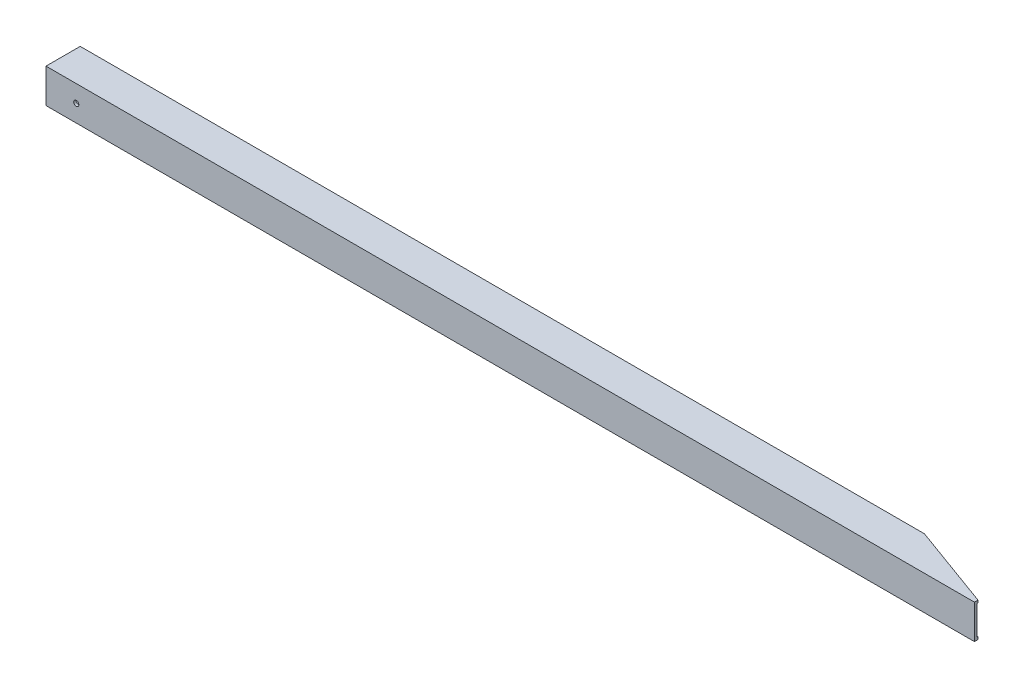
SolidWorks part; units mm, degrees
material "6061 Alloy"
ref_plane "Front Plane" through (0, 0, 0) normal (0, 0, 1) x (1, 0, 0)
ref_plane "Top Plane" through (0, 0, 0) normal (0, 1, 0) x (1, 0, 0)
ref_plane "Right Plane" through (0, 0, 0) normal (1, 0, 0) x (0, 0, -1)
sketch "Sketch1" plane through (0, 0, 0) normal (1, 0, 0) x (0, 0, -1)
  line L0 (3.175, 3.175) -> (3.175, 41.275)
  line L1 (0, 0) -> (44.45, 0)
  line L2 (0, 0) -> (0, 44.45)
  line L3 (0, 44.45) -> (44.45, 44.45)
  line L4 (44.45, 0) -> (44.45, 44.45)
  line L5 (3.175, 41.275) -> (41.275, 41.275)
  line L6 (41.275, 3.175) -> (41.275, 41.275)
  line L7 (3.175, 3.175) -> (41.275, 3.175)
  dimension "D2" = 44.45
  dimension "D1" = 3.175
extrude "Boss-Extrude1" add sketch "Sketch1" along normal blind 1219.2
sketch "Sketch2" plane through (0, 44.45, 0) normal (0, 1, 0) x (1, 0, 0)
  line L0 (1219.2, 0) -> (1097.0746, 44.45)
  line L1 (1219.2, 44.45) -> (0, 44.45) construction
  line L2 (1097.0746, 44.45) -> (1219.2, 44.45)
  line L3 (1219.2, 44.45) -> (1219.2, 0)
  line L4 (1219.2, 0) -> (0, 0) construction
  dimension "D1" = 20
extrude "Cut-Extrude1" cut sketch "Sketch2" against normal through all
hole_wizard "1/4 Clearance Hole1" positions "Sketch3" profile "Sketch4" hole size "1/4" standard "ANSI Inch" end condition through all
sketch "Sketch3" plane through (0, 0, 0) normal (0, 0, 1) x (1, 0, 0)
  line L0 (0, 44.45) -> (0, 0) construction
  point P0 (39.37, 22.225)
  point P5 (0, 22.225)
  dimension "D1" = 39.37
sketch "Sketch4" plane through (39.37, 22.225, 0) normal (1, 0, 0) x (0, -1, 0)
  line L0 (0, 0) -> (0, 44.45)
  line L1 (0, 44.45) -> (3.3782, 44.45)
  line L2 (3.3782, 44.45) -> (3.3782, 0)
  line L5 (3.3782, 0) -> (0, 0)
  line L11 (0, -6.35) -> (0, 107.95) construction
  dimension "Thru Hole Dia." = 6.7564
  dimension "Thru Hole Depth" = 44.45
sketch "Sketch5" plane through (0, 44.45, 0) normal (0, 1, 0) x (1, 0, 0)
  line L0 (1219.2, 0) -> (1206.5, 0)
  line L1 (1219.2, 0) -> (0, 0) construction
  line L2 (1206.5, 0) -> (1206.5, 4.6224)
  line L3 (1097.0746, 44.45) -> (1219.2, 0) construction
  line L4 (1206.5, 4.6224) -> (1219.2, 0)
  dimension "D1" = 12.7
extrude "Cut-Extrude2" cut sketch "Sketch5" against normal through all
